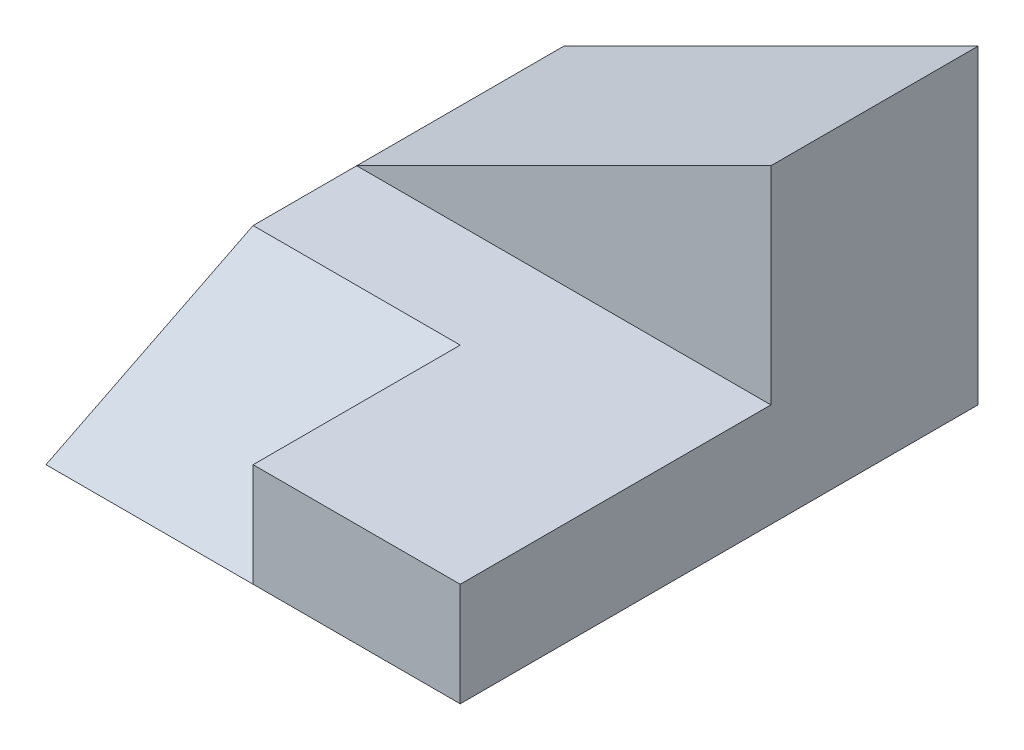
SolidWorks part; units mm, degrees
ref_plane "Front Plane" through (0, 0, 0) normal (0, 0, 1) x (1, 0, 0)
ref_plane "Top Plane" through (0, 0, 0) normal (0, 1, 0) x (1, 0, 0)
ref_plane "Right Plane" through (0, 0, 0) normal (1, 0, 0) x (0, 0, -1)
sketch "Sketch1" plane through (0, 0, 0) normal (1, 0, 0) x (0, 0, -1)
  line L0 (25, 0) -> (-25, 0)
  line L1 (-25, 0) -> (-25, 10)
  line L2 (-25, 10) -> (5, 10)
  line L3 (5, 10) -> (5, 30)
  line L4 (5, 30) -> (25, 30)
  line L5 (25, 30) -> (25, 0)
  point P4 (0, 0)
  dimension "D1" = 10
  dimension "D2" = 30
  dimension "D3" = 20
  dimension "D4" = 50
extrude "Boss-Extrude1" add sketch "Sketch1" against normal blind 40
sketch "Sketch3" plane through (0, 0, -5) normal (0, 0, 1) x (1, 0, 0)
  line L0 (0, 30) -> (0, 10) construction
  line L2 (0, 30) -> (0, 10)
  line L5 (-40, 30) -> (-40, 10)
  line L6 (-40, 30) -> (0, 30)
  line L7 (0, 30) -> (-40, 10)
  line L8 (-40, 10) -> (0, 10) construction
  point P4 (-50, 10)
  line M5 (0, 30) -> (-40, 30)
  line M6 (-40, 30) -> (-40, 10)
extrude "Cut-Extrude6" cut sketch "Sketch3" against normal blind 50 contours L7 M5 M6
sketch "Sketch5" plane through (-40, 0, 0) normal (-1, 0, 0) x (0, 0, 1)
  line L0 (5, 10) -> (5, 0)
  line L1 (-5, 10) -> (25, 10) construction
  line L2 (25, 0) -> (-25, 0) construction
  line L3 (5, 10) -> (25, 0)
  line L4 (25, 0) -> (25, 10)
  line L5 (25, 10) -> (5, 10)
  line M5 (25, 0) -> (25, 10)
  line M6 (25, 10) -> (-5, 10)
  dimension "D1" = 10
extrude "Cut-Extrude7" cut sketch "Sketch5" against normal blind 20 contours L3 M6 M5
